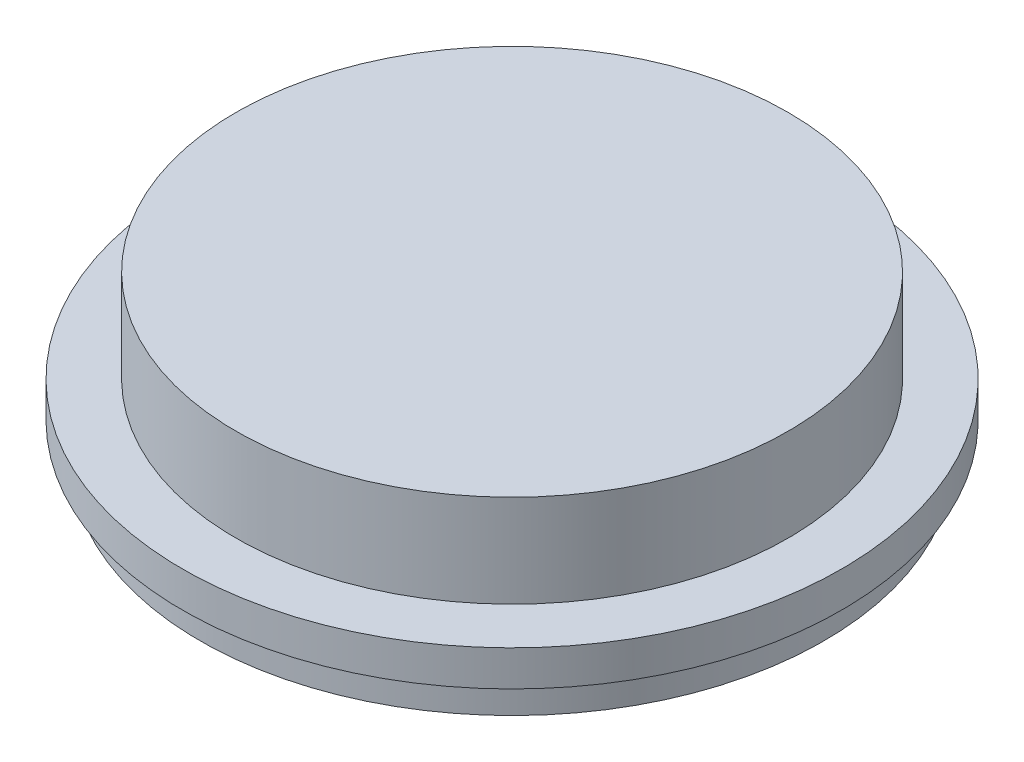
SolidWorks part; units mm, degrees
material "Epoxy, Unfilled"
ref_plane "Front Plane" through (0, 0, 0) normal (0, 0, 1) x (1, 0, 0)
ref_plane "Top Plane" through (0, 0, 0) normal (0, 1, 0) x (1, 0, 0)
ref_plane "Right Plane" through (0, 0, 0) normal (1, 0, 0) x (0, 0, -1)
sketch "Sketch1" plane through (0, 0, 0) normal (0, 0, 1) x (1, 0, 0)
  line L0 (0, 0) -> (0, 25.4) construction
sketch "Sketch2" plane through (0, 0, 0) normal (0, 0, 1) x (1, 0, 0)
  line L0 (0, 0) -> (49.2125, 0)
  line L1 (49.2125, 0) -> (49.2125, -16.51)
  line L2 (49.2125, -16.51) -> (58.7375, -16.51)
  line L3 (58.7375, -16.51) -> (58.7375, -22.86)
  line L4 (58.7375, -22.86) -> (55.5625, -22.86)
  line L5 (55.5625, -22.86) -> (55.5625, -29.21)
  line L6 (55.5625, -29.21) -> (49.2125, -29.21)
  line L7 (49.2125, -29.21) -> (49.2125, -22.86)
  line L8 (49.2125, -22.86) -> (42.8625, -22.86)
  line L9 (42.8625, -22.86) -> (42.8625, -6.35)
  line L10 (42.8625, -6.35) -> (0, -6.35)
  line L11 (0, -6.35) -> (0, 0)
revolve "Revolve1" add sketch "Sketch2" angle 360 about L0
